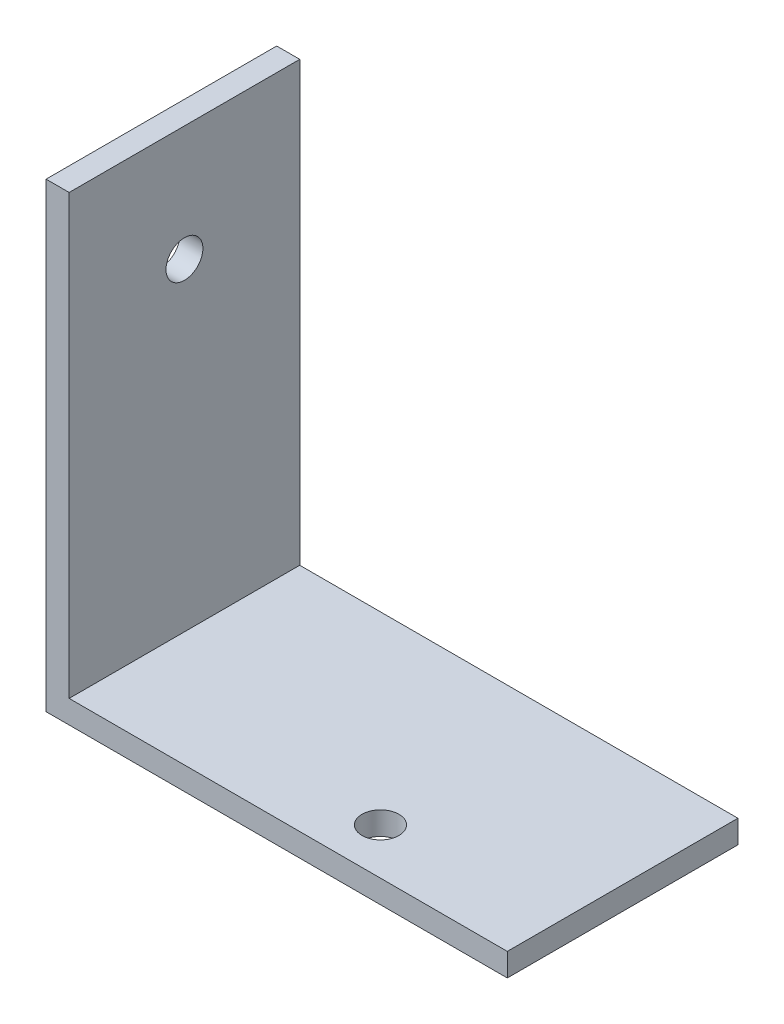
SolidWorks part; units mm, degrees
material "1060 Сплав"
ref_plane "Спереди" through (0, 0, 0) normal (0, 0, 1) x (1, 0, 0)
ref_plane "Сверху" through (0, 0, 0) normal (0, 1, 0) x (1, 0, 0)
ref_plane "Справа" through (0, 0, 0) normal (1, 0, 0) x (0, 0, -1)
sketch "Эскиз1" plane through (0, 0, 0) normal (0, 0, 1) x (1, 0, 0)
  line L0 (0, 0) -> (40, 0)
  line L1 (40, 0) -> (40, 2)
  line L2 (40, 2) -> (2, 2)
  line L3 (2, 2) -> (2, 40)
  line L4 (2, 40) -> (0, 40)
  line L5 (0, 40) -> (0, 0)
  dimension "D1" = 40
  dimension "D2" = 2
  dimension "D3" = 40
extrude "Бобышка-Вытянуть1" add sketch "Эскиз1" along normal blind 20
sketch "Эскиз3" plane through (0, 0, 0) normal (-1, 0, 0) x (0, 0, 1)
  line L0 (10, 40) -> (10, 0) construction
  line L1 (20, 40) -> (0, 40) construction
  line L2 (20, 0) -> (0, 0) construction
  circle A0 centre (10, 30) radius 1.6
  dimension "D1" = 3.2
  dimension "D2" = 10
extrude "Вырез-Вытянуть2" cut sketch "Эскиз3" against normal through all
sketch "Эскиз4" plane through (0, 0, 0) normal (0, -1, 0) x (1, 0, 0)
  arc A0 (23.4, 16) -> (26.6, 16) centre (25, 16) ccw construction
  arc A1 (23.4, 16) -> (26.6, 16) centre (25, 16) ccw construction
  circle A2 centre (25, 16) radius 1.6
extrude "Вырез-Вытянуть3" cut sketch "Эскиз4" against normal through all
